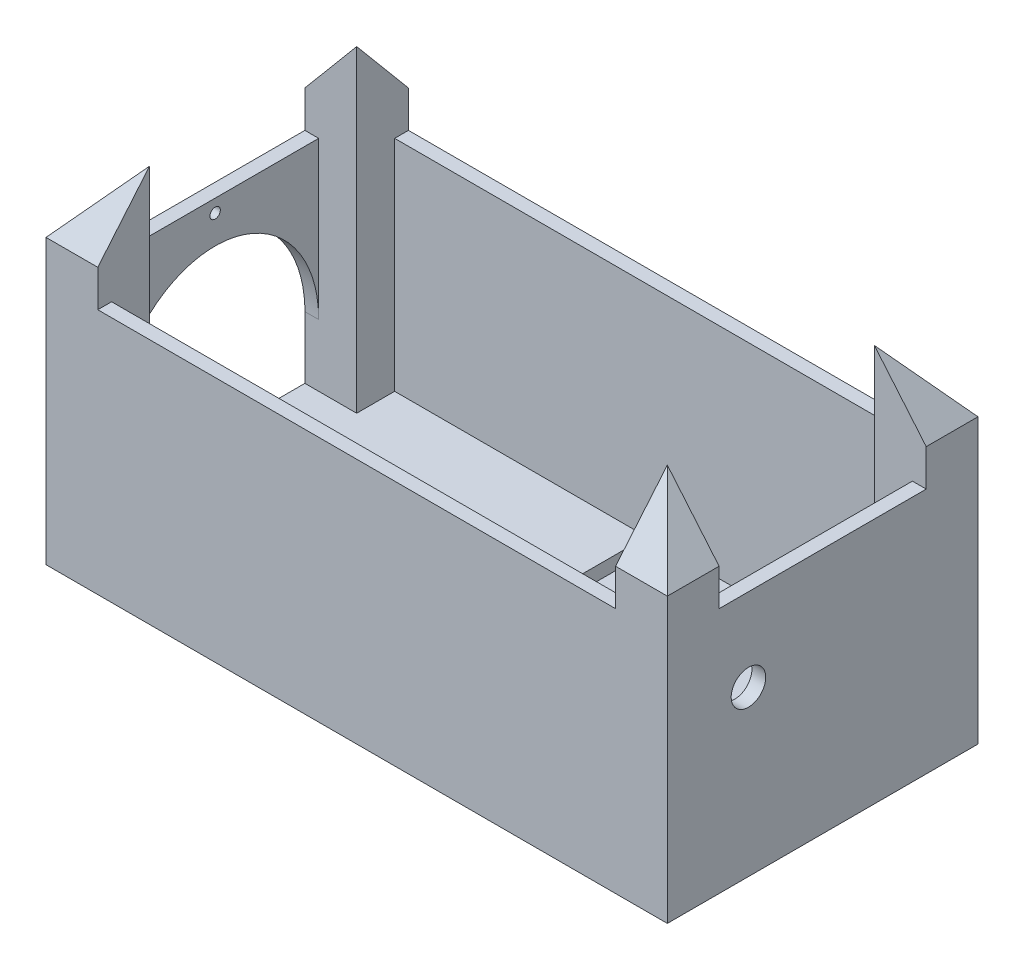
SolidWorks part; units mm, degrees
ref_plane "Front Plane" through (0, 0, 0) normal (0, 0, 1) x (1, 0, 0)
ref_plane "Top Plane" through (0, 0, 0) normal (0, 1, 0) x (1, 0, 0)
ref_plane "Right Plane" through (0, 0, 0) normal (1, 0, 0) x (0, 0, -1)
sketch "Sketch1" plane through (0, 0, 0) normal (0, 1, 0) x (1, 0, 0)
  line L1 (0, 0) -> (180, 0)
  line L2 (0, 0) -> (0, -90)
  line L3 (0, -90) -> (180, -90)
  line L4 (180, 0) -> (180, -90)
  dimension "D1" = 180
  dimension "D2" = 90
extrude "Boss-Extrude1" add sketch "Sketch1" along normal blind 71.47
shell "Shell1" thickness 4
sketch "Sketch2" plane through (180, 0, 0) normal (1, 0, 0) x (0, 0, -1)
  line L1 (-90, 71.47) -> (-90, 0) construction
  line L2 (-90, 0) -> (0, 0) construction
  circle A0 centre (-66.5, 47.5) radius 5
  dimension "D1" = 10
  dimension "D2" = 47.5
  dimension "D3" = 23.5
extrude "Cut-Extrude1" cut sketch "Sketch2" against normal up to surface (4 mm away) up to face at (176, 37.735, 45)
sketch "Sketch4" plane through (0, 4, 0) normal (0, 1, 0) x (1, 0, 0)
  line L0 (176, -45) -> (4, -45) construction
  line L1 (176, -86) -> (176, -4) construction
  line L2 (4, -4) -> (4, -86) construction
  line L3 (90, -86) -> (90, -4) construction
  line L4 (4, -86) -> (176, -86) construction
  line L5 (176, -4) -> (4, -4) construction
  circle A0 centre (90, -45) radius 2
  dimension "D1" = 4
extrude "Cut-Extrude2" cut sketch "Sketch4" against normal through all
sketch "Sketch7" plane through (0, 4, 0) normal (0, 1, 0) x (1, 0, 0)
  line L1 (0, 0) -> (15, 0)
  line L2 (0, 0) -> (0, -15)
  line L3 (0, -15) -> (15, -15)
  line L4 (15, 0) -> (15, -15)
  line L5 (180, 0) -> (165, 0)
  line L6 (180, 0) -> (180, -15)
  line L7 (180, -15) -> (165, -15)
  line L8 (165, 0) -> (165, -15)
  line L9 (180, -90) -> (165, -90)
  line L10 (180, -90) -> (180, -75)
  line L11 (180, -75) -> (165, -75)
  line L12 (165, -90) -> (165, -75)
  line L13 (0, -90) -> (15, -90)
  line L14 (0, -90) -> (0, -75)
  line L15 (0, -75) -> (15, -75)
  line L16 (15, -90) -> (15, -75)
  dimension "D1" = 15
  dimension "D2" = 15
  dimension "D3" = 15
  dimension "D4" = 15
  dimension "D5" = 15
  dimension "D6" = 15
  dimension "D7" = 15
  dimension "D8" = 15
extrude "Boss-Extrude3" add sketch "Sketch7" along normal blind 98.12
sketch "Sketch8" plane through (0, 0, 90) normal (0, 0, 1) x (1, 0, 0)
  line L0 (0, 82.12) -> (90, 189.3778)
  line L1 (90, 189.3778) -> (180, 82.12)
  line L2 (180, 82.12) -> (180, 229.2704)
  line L3 (180, 229.2704) -> (-17.5941, 229.2704)
  line L4 (-17.5941, 229.2704) -> (-17.5941, 82.12)
  line L5 (-17.5941, 82.12) -> (0, 82.12)
  line L6 (0, 102.12) -> (0, 0) construction
  line L7 (180, 102.12) -> (180, 0) construction
  line L8 (165, 102.12) -> (180, 102.12) construction
  line L9 (0, 102.12) -> (15, 102.12) construction
  point P12 (172.5, 102.12)
  point P13 (-8.797, 82.12)
  dimension "D1" = 40
  dimension "D2" = 40
  dimension "D3" = 0
  dimension "D4" = 0
  dimension "D5" = 20
  dimension "D6" = 20
  dimension "D7" = 147.1504
  dimension "D8" = 17.5941
extrude "Cut-Extrude4" cut sketch "Sketch8" against normal through all
sketch "Sketch10" plane through (180, 0, 0) normal (1, 0, 0) x (0, 0, -1)
  line L0 (-90, 82.12) -> (-45, 135.7489)
  line L1 (-45, 135.7489) -> (0, 82.12)
  line L2 (0, 82.12) -> (0, 148.6326)
  line L3 (0, 148.6326) -> (-124.3013, 148.6326)
  line L4 (-124.3013, 148.6326) -> (-124.3013, 82.12)
  line L5 (-124.3013, 82.12) -> (-90, 82.12)
  line L6 (-90, 99.9963) -> (-90, 82.12) construction
  line L7 (0, 99.9963) -> (0, 82.12) construction
  line L8 (-75, 71.47) -> (-15, 71.47) construction
  dimension "D1" = 40
  dimension "D2" = 40
  dimension "D3" = 0
  dimension "D4" = 90
  dimension "D5" = 0
  dimension "D6" = 12.8837
  dimension "D7" = 34.3013
extrude "Cut-Extrude5" cut sketch "Sketch10" against normal through all
hole_wizard "M3x0.5 Tapped Hole1" positions "Sketch12" profile "Sketch13" tap size "M3x0.5" standard "ANSI Metric"
sketch "Sketch12" plane through (0, 0, 0) normal (0, -1, 0) x (-1, 0, 0)
  line L0 (-180, 0) -> (0, 0) construction
  line L1 (-180, -90) -> (-180, 0) construction
  line L2 (0, 0) -> (0, -90) construction
  line L3 (0, -90) -> (-180, -90) construction
  point P0 (-172.5, -7.5)
  point P2 (-7.5, -7.5)
  point P4 (-7.5, -82.5)
  point P6 (-172.5, -82.5)
  dimension "D1" = 7.5
  dimension "D2" = 7.5
  dimension "D3" = 7.5
  dimension "D4" = 7.5
  dimension "D5" = 7.5
  dimension "D6" = 7.5
  dimension "D7" = 7.5
  dimension "D8" = 7.5
sketch "Sketch13" plane through (172.5, 0, 7.5) normal (1, 0, 0) x (0, 0, -1)
  line L0 (0, 0) -> (0, 8.2511)
  line L1 (0, 8.2511) -> (1.25, 7.5)
  line L2 (1.25, 7.5) -> (1.25, 0)
  line L5 (1.25, 0) -> (0, 0)
  line L10 (0, 8.2511) -> (-1.25, 7.5) construction
  line L11 (0, -6.35) -> (0, 107.95) construction
  dimension "Tap Drill Dia." = 2.5
  dimension "Tap Drill Depth" = 7.5
  dimension "Drill Angle" = 118
sketch "Sketch17" plane through (0, 4, 0) normal (0, 1, 0) x (1, 0, 0)
  line L0 (165, -4) -> (15, -4) construction
  line L1 (4, -4) -> (88, -4)
  line L2 (4, -4) -> (4, -43)
  line L3 (4, -43) -> (88, -43)
  line L4 (88, -4) -> (88, -43)
  line L5 (4, -15) -> (4, -75) construction
  line L6 (176, -45) -> (4, -45) construction
  line L7 (176, -75) -> (176, -15) construction
  line L8 (90, -4) -> (90, -86) construction
  line L9 (15, -86) -> (165, -86) construction
  line L10 (176, -4) -> (92, -4)
  line L11 (176, -4) -> (176, -43)
  line L12 (176, -43) -> (92, -43)
  line L13 (92, -4) -> (92, -43)
  line L14 (176, -86) -> (176, -47)
  line L15 (176, -47) -> (92, -47)
  line L16 (176, -86) -> (92, -86)
  line L17 (92, -86) -> (92, -47)
  line L18 (4, -86) -> (4, -47)
  line L19 (4, -86) -> (88, -86)
  line L20 (88, -86) -> (88, -47)
  line L21 (4, -47) -> (88, -47)
  circle A0 centre (90, -45) radius 2 construction
  dimension "D1" = 0
  dimension "D2" = 0
  dimension "D3" = 2
  dimension "D4" = 2
extrude "Boss-Extrude5" add sketch "Sketch17" along normal blind 4
sketch "Sketch15" plane through (0, 0, 0) normal (-1, 0, 0) x (0, 0, 1)
  line L0 (15, 8) -> (43, 8) construction
  line L1 (45, 59.47) -> (45, 40.2823) construction
  line L3 (0, 82.12) -> (0, 0) construction
  line L5 (15, 26) -> (15, 8)
  line L6 (15, 8) -> (75, 8)
  line L7 (75, 26) -> (75, 8)
  line L8 (90, 82.12) -> (90, 0) construction
  ellipse E0 centre (45, 26) end of major axis (45, -7.47) minor radius 30 (75, 26) -> (15, 26) ccw
  dimension "D1" = 18
  dimension "D2" = 15
  dimension "D3" = 15
  dimension "D4" = 0
  dimension "D5" = 18
  dimension "D6" = 30
  dimension "D7" = 66.94
extrude "Cut-Extrude6" cut sketch "Sketch15" against normal up to surface (4 mm away) up to face at (4, 22.8675, 45)
sketch "Sketch18" plane through (0, 0, 0) normal (-1, 0, 0) x (0, 0, 1)
  line L0 (5.9, 7.75) -> (84.1, 7.75) construction
  line L1 (45, 8) -> (45, 47.0126) construction
  line L2 (15, 8) -> (75, 8) construction
  line L3 (15, 26) -> (15, 8) construction
  line L4 (75, 8) -> (75, 26) construction
  circle A0 centre (82.75, 7.75) radius 1.5
  circle A2 centre (45, 67.72) radius 1.5
  circle A3 centre (7.25, 7.75) radius 1.5
  point P12 (45, 7.75)
  dimension "D1" = 3
  dimension "D3" = 59.72
  dimension "D6" = 7.75
  dimension "D7" = 0.25
  dimension "D8" = 3
  dimension "D9" = 3
  dimension "D2" = 0.25
  dimension "D4" = 9.1
  dimension "D5" = 7.75
extrude "Cut-Extrude7" cut sketch "Sketch18" against normal blind 10
